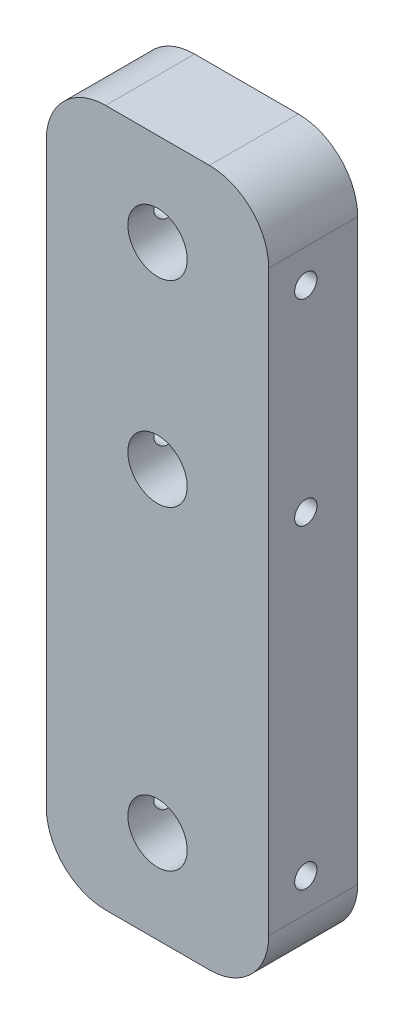
SolidWorks part; units mm, degrees
ref_plane "Front Plane" through (0, 0, 0) normal (0, 0, 1) x (1, 0, 0)
ref_plane "Top Plane" through (0, 0, 0) normal (0, 1, 0) x (1, 0, 0)
ref_plane "Right Plane" through (0, 0, 0) normal (1, 0, 0) x (0, 0, -1)
sketch "Sketch1" plane through (0, 0, 0) normal (0, 0, 1) x (1, 0, 0)
  line L1 (-15, -46.99) -> (15, -46.99)
  line L2 (-15, -46.99) -> (-15, 46.99)
  line L3 (-15, 46.99) -> (15, 46.99)
  line L4 (15, -46.99) -> (15, 46.99)
  line L5 (-15, -46.99) -> (15, 46.99) construction
  line L6 (-15, 46.99) -> (15, -46.99) construction
  point P0 (0, 0)
  dimension "D1" = 30
  dimension "D2" = 93.98
extrude "Boss-Extrude1" add sketch "Sketch1" along normal blind 12
fillet "Fillet1" radius 8 4 edges at (-15, 46.99, 6) (-15, -46.99, 6) (15, -46.99, 6) (15, 46.99, 6)
sketch "Sketch2" plane through (0, 0, 12) normal (0, 0, 1) x (1, 0, 0)
  line L0 (0, 46.99) -> (0, -46.99) construction
  line L1 (7, 46.99) -> (-7, 46.99) construction
  line L2 (-7, -46.99) -> (7, -46.99) construction
  circle A0 centre (0, 7.99) radius 4
  circle A1 centre (0, 34.49) radius 4
  circle A2 centre (0, -34.4949) radius 4
  dimension "D1" = 8
  dimension "D2" = 39
extrude "Cut-Extrude1" cut sketch "Sketch2" against normal blind 8
sketch "Sketch3" plane through (-15, 0, 0) normal (-1, 0, 0) x (0, 0, 1)
  line L0 (7, 46.99) -> (7, -46.99) construction
  line L1 (0, 46.99) -> (12, 46.99) construction
  line L2 (12, -46.99) -> (0, -46.99) construction
  line L3 (12, 38.99) -> (12, 46.99) construction
  line L4 (4, 34.49) -> (7, 34.49) construction
  line L5 (4, 30.49) -> (4, 38.49) construction
  line L7 (4, 7.99) -> (7, 7.99) construction
  line L8 (4, -34.4949) -> (7, -34.4949) construction
  line L9 (4, -38.4949) -> (4, -30.4949) construction
  circle A0 centre (7, 34.49) radius 1.5
  circle A1 centre (7, 7.99) radius 1.5
  circle A2 centre (7, -34.4949) radius 1.5
  point P8 (12, 42.99)
  dimension "D2" = 3
  dimension "D1" = 5
extrude "Cut-Extrude2" cut sketch "Sketch3" against normal through all
sketch "Sketch4" plane through (0, 0, 0) normal (0, 0, -1) x (-1, 0, 0)
  line L0 (0, -46.99) -> (0, 46.99) construction
  line L1 (7, -46.99) -> (-7, -46.99) construction
  line L2 (-7, 46.99) -> (7, 46.99) construction
  circle A0 centre (0, -26.99) radius 2
  circle A1 centre (0, 26.99) radius 2
  dimension "D1" = 4
  dimension "D2" = 20
  dimension "D3" = 20
extrude "Cut-Extrude3" cut sketch "Sketch4" against normal blind 2.5
